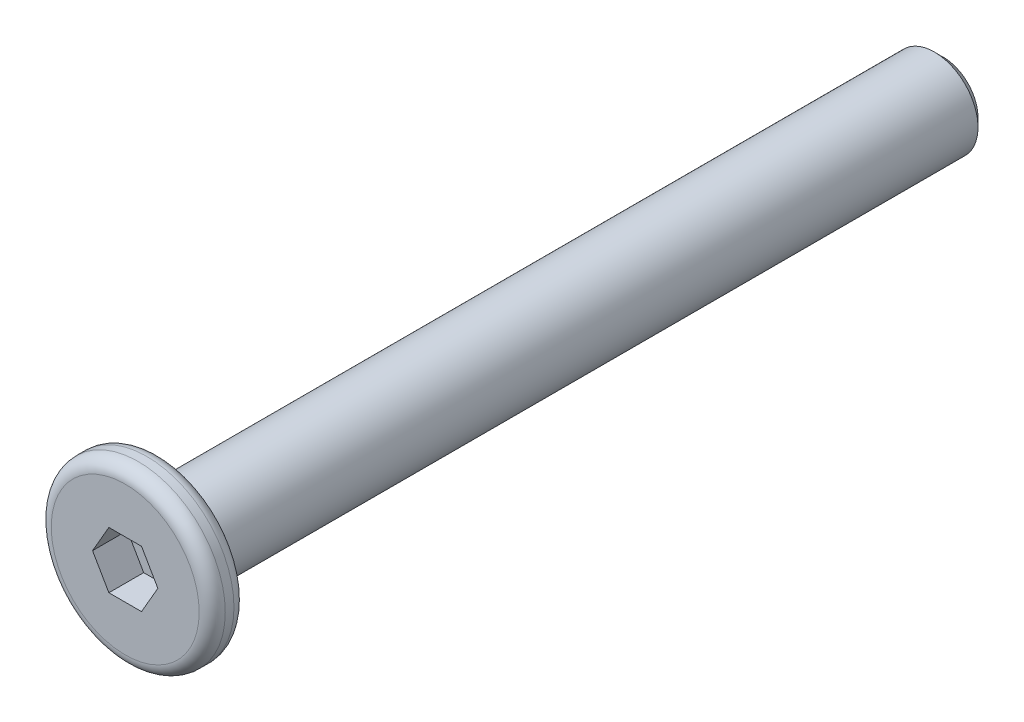
SolidWorks part; units mm, degrees
ref_plane "前视基准面" through (0, 0, 0) normal (0, 0, 1) x (1, 0, 0)
ref_plane "上视基准面" through (0, 0, 0) normal (0, 1, 0) x (1, 0, 0)
ref_plane "右视基准面" through (0, 0, 0) normal (1, 0, 0) x (0, 0, -1)
sketch "草图1" plane through (0, 0, 0) normal (0, 0, 1) x (1, 0, 0)
  circle A0 centre (0, 0) radius 2
  dimension "D1" = 4
extrude "凸台-拉伸1" add sketch "草图1" along normal mid plane 0.8
sketch "草图2" plane through (0, 0, -0.4) normal (0, 0, -1) x (-1, 0, 0)
  circle A0 centre (0, 0) radius 1
  dimension "D1" = 2
extrude "凸台-拉伸2" add sketch "草图2" along normal blind 18
chamfer "倒角1" distance 0.2 angle 45 1 edges at (-1, 0, -18.4)
sketch "草图3" plane through (0, 0, 0.4) normal (0, 0, 1) x (1, 0, 0)
  line L1 (0.7506, 0) -> (0.3753, 0.65)
  line L2 (0.3753, 0.65) -> (-0.3753, 0.65)
  line L3 (-0.3753, 0.65) -> (-0.7506, 0)
  line L4 (-0.7506, 0) -> (-0.3753, -0.65)
  line L5 (-0.3753, -0.65) -> (0.3753, -0.65)
  line L6 (0.3753, -0.65) -> (0.7506, 0)
  circle A0 centre (0, 0) radius 0.65 construction
  dimension "D1" = 1.3
extrude "切除-拉伸1" cut sketch "草图3" against normal blind 0.8
fillet "圆角2" radius 0.3 2 edges at (2, 0, -0.4) (2, 0, 0.4)
